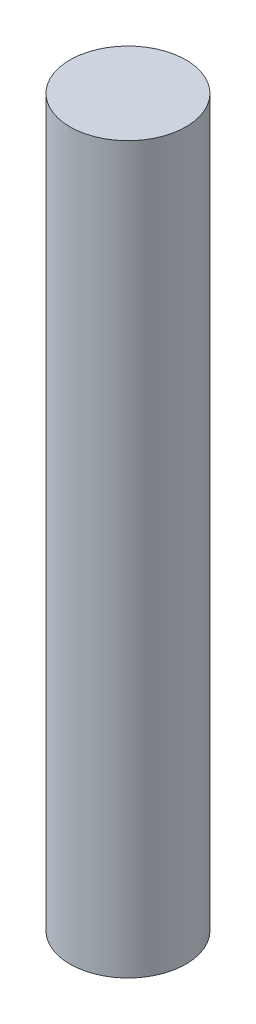
SolidWorks part; units mm, degrees
ref_plane "Alzado" through (0, 0, 0) normal (0, 0, 1) x (1, 0, 0)
ref_plane "Planta" through (0, 0, 0) normal (0, 1, 0) x (1, 0, 0)
ref_plane "Vista lateral" through (0, 0, 0) normal (1, 0, 0) x (0, 0, -1)
sketch "Croquis1" plane through (0, 0, 0) normal (0, 1, 0) x (1, 0, 0)
  circle A0 centre (0, 0) radius 4
  dimension "D1" = 8
extrude "Saliente-Extruir1" add sketch "Croquis1" along normal blind 50
